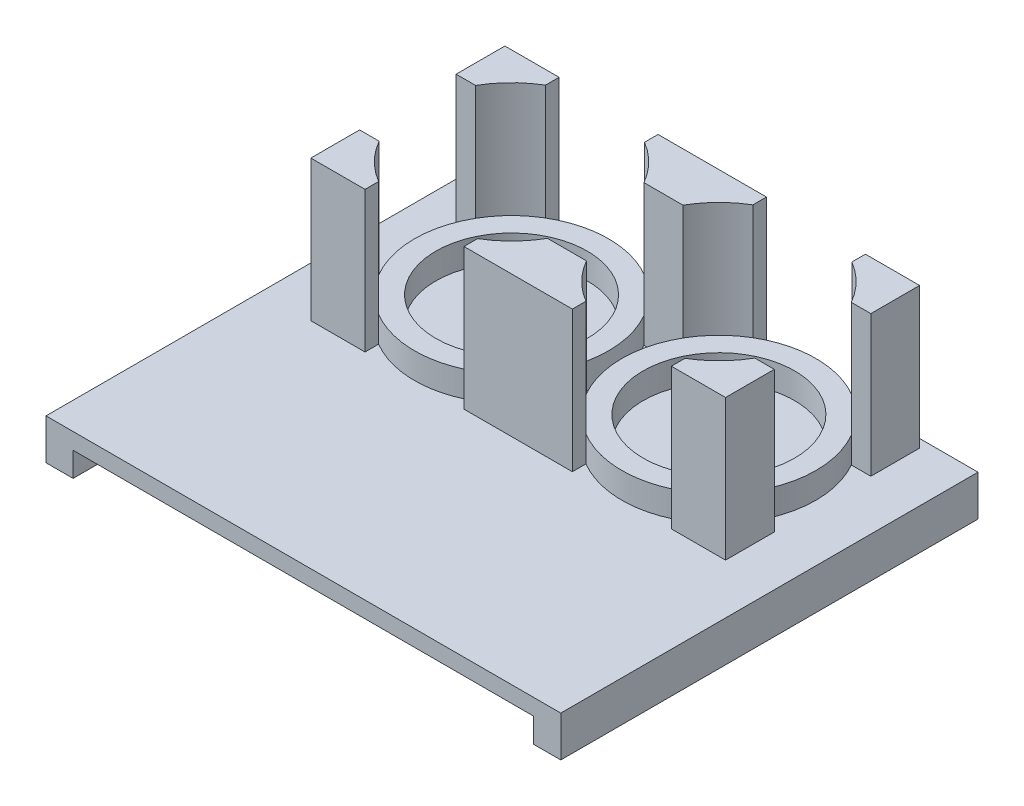
SolidWorks part; units mm, degrees
ref_plane "Front Plane" through (0, 0, 0) normal (0, 0, 1) x (1, 0, 0)
ref_plane "Top Plane" through (0, 0, 0) normal (0, 1, 0) x (1, 0, 0)
ref_plane "Right Plane" through (0, 0, 0) normal (1, 0, 0) x (0, 0, -1)
sketch "Sketch1" plane through (0, 0, 0) normal (0, 1, 0) x (1, 0, 0)
  line L0 (-42.5, 38.5) -> (42.5, 38.5)
  line L1 (0, -38.5) -> (0, 38.5) construction
  line L2 (-42.5, -38.5) -> (42.5, -38.5)
  line L3 (-42.5, 38.5) -> (-42.5, -38.5)
  line L4 (42.5, 38.5) -> (42.5, -38.5)
  point P3 (0, 38.5)
  point P7 (0, 0)
  point P11 (0, -38.5)
  dimension "D1" = 85
  dimension "D3" = 77
extrude "Boss-Extrude1" add sketch "Sketch1" along normal blind 3
sketch "Sketch3" plane through (0, 3, 0) normal (0, 1, 0) x (1, 0, 0)
  line L0 (-19.1333, 19.0489) -> (19.1333, 19.0489) construction
  line L2 (-1.263, 29.4507) -> (-1.0184, 29.4507)
  line L3 (20.9899, 39.6427) -> (-1.0184, 29.4507)
  line L5 (2.6231, 8.7736) -> (17.2768, -1.5448)
  line L6 (17.2768, -1.5448) -> (36.0397, 7.1443)
  line L7 (36.0397, 7.1443) -> (37.8963, 27.738)
  line L8 (37.8963, 27.738) -> (20.9899, 39.6427)
  line L9 (-19.2063, 39.726) -> (-37.0767, 29.3243)
  line L10 (-37.0767, 29.3243) -> (-37.0037, 8.6472)
  line L11 (-37.0037, 8.6472) -> (-19.0603, -1.6281)
  line L12 (-19.0603, -1.6281) -> (-1.1899, 8.7736)
  line L13 (-1.1899, 8.7736) -> (-1.263, 29.4507)
  line L14 (-1.263, 29.4507) -> (-19.2063, 39.726)
  line L15 (-1.1899, 8.7736) -> (2.6231, 8.7736)
  line L16 (0.7975, 15.0979) -> (-1.1775, -6.8103) [skipped]
  circle A0 centre (19.1333, 19.0489) radius 17.907
  circle A1 centre (-19.1333, 19.0489) radius 17.907
  circle A2 centre (-19.1333, 19.0489) radius 13.97
  circle A3 centre (19.1333, 19.0489) radius 13.97
  circle A4 centre (19.1333, 19.0489) radius 17.907 construction
  circle A5 centre (-19.1333, 19.0489) radius 17.907 construction
  point P4 (0, 0)
  dimension "D1" = 35.814
  dimension "D3" = 27.94
extrude "Boss-Extrude3" add sketch "Sketch3" along normal blind 4.7625
sketch "Sketch4" plane through (0, 3, 0) normal (0, 1, 0) x (1, 0, 0)
  line L0 (-19.1333, 36.9559) -> (19.1333, 36.9559) construction
  line L1 (0, 36.9559) -> (-10, 36.9559)
  line L2 (-10, 36.9559) -> (-10, 34.4516)
  line L3 (0, 36.9559) -> (10, 36.9559)
  line L4 (10, 36.9559) -> (10, 34.4516)
  line L5 (-1.2263, 19.0489) -> (16.6975, 19.0489) construction
  line L6 (-3.5987, 27.9559) -> (3.5987, 27.9559)
  line L7 (-3.5987, 10.1419) -> (3.5987, 10.1419)
  line L8 (10, 1.1419) -> (10, 3.6463)
  line L9 (0, 1.1419) -> (10, 1.1419)
  line L10 (-10, 1.1419) -> (-10, 3.6463)
  line L11 (0, 1.1419) -> (-10, 1.1419)
  line L12 (0, 36.9559) -> (0, 27.9559)
  line L13 (0, 10.1419) -> (0, 1.1419)
  line L14 (-19.1333, 36.9559) -> (-19.1333, 19.0489) construction
  line L15 (19.1333, 36.9559) -> (19.1333, 19.0489) construction
  line L16 (-38.2667, 10.1419) -> (-38.2667, 1.1419)
  line L17 (-38.2667, 1.1419) -> (-28.2667, 1.1419)
  line L18 (-28.2667, 1.1419) -> (-28.2667, 3.6463)
  line L19 (-38.2667, 36.9559) -> (-38.2667, 27.9559)
  line L20 (-38.2667, 36.9559) -> (-28.2667, 36.9559)
  line L21 (-28.2667, 36.9559) -> (-28.2667, 34.4516)
  line L22 (-38.2667, 27.9559) -> (-34.668, 27.9559)
  line L23 (-38.2667, 10.1419) -> (-34.668, 10.1419)
  line L24 (28.2667, 1.1419) -> (28.2667, 3.6463)
  line L25 (38.2667, 1.1419) -> (28.2667, 1.1419)
  line L26 (38.2667, 10.1419) -> (38.2667, 1.1419)
  line L27 (38.2667, 27.9559) -> (34.668, 27.9559)
  line L28 (28.2667, 36.9559) -> (28.2667, 34.4516)
  line L29 (38.2667, 36.9559) -> (28.2667, 36.9559)
  line L30 (38.2667, 36.9559) -> (38.2667, 27.9559)
  line L31 (38.2667, 10.1419) -> (34.668, 10.1419)
  circle A0 centre (-19.1333, 19.0489) radius 17.907 construction
  circle A1 centre (19.1333, 19.0489) radius 17.907 construction
  arc A2 (10, 34.4516) -> (3.5987, 27.9559) centre (19.1333, 19.0489) ccw
  circle A3 centre (-19.1333, 19.0489) radius 17.907 construction
  circle A4 centre (19.1333, 19.0489) radius 17.907 construction
  arc A5 (-3.5987, 27.9559) -> (-10, 34.4516) centre (-19.1333, 19.0489) ccw
  arc A6 (-3.5987, 10.1419) -> (-10, 3.6463) centre (-19.1333, 19.0489) cw
  arc A7 (10, 3.6463) -> (3.5987, 10.1419) centre (19.1333, 19.0489) cw
  arc A8 (-34.668, 10.1419) -> (-28.2667, 3.6463) centre (-19.1333, 19.0489) ccw
  arc A9 (-34.668, 27.9559) -> (-28.2667, 34.4516) centre (-19.1333, 19.0489) cw
  arc A10 (34.668, 10.1419) -> (28.2667, 3.6463) centre (19.1333, 19.0489) cw
  arc A11 (34.668, 27.9559) -> (28.2667, 34.4516) centre (19.1333, 19.0489) ccw
  point P0 (0, 27.9559)
  point P4 (0, 0)
  point P29 (0, 10.1419)
  circle M6 centre (19.1333, 19.0489) radius 17.907
  circle M7 centre (-19.1333, 19.0489) radius 17.907
  dimension "D3" = 9
  dimension "D2" = 10
extrude "Boss-Extrude7" add sketch "Sketch4" along normal blind 26 contours L19 L22 L21 L20 M7 | L23 L16 L17 L18 M7 | L13 L7 L10 L11 M7 | L7 L13 L9 L8 M6 | L12 L1 L2 L6 M7 | L3 L12 L6 L4 M6 | L30 L29 L28 L27 M6 | L26 L31 L24 L25 M6
sketch "Sketch6" plane through (-42.5, 0, 0) normal (-1, 0, 0) x (0, 0, 1)
  line L0 (-38.5, 3) -> (-38.5, -4.5)
  line L1 (38.5, 3) -> (38.5, -4.5)
  line L2 (-38.5, 3) -> (38.5, 3) construction
  line L3 (-38.5, 3) -> (38.5, 3)
  line L4 (-38.5, -4.5) -> (38.5, -4.5)
  dimension "D1" = 7.5
extrude "Boss-Extrude8" add sketch "Sketch6" along normal blind 5
mirror "Mirror1" about plane through (0, 0, 0) normal (1, 0, 0) of "Boss-Extrude8"
